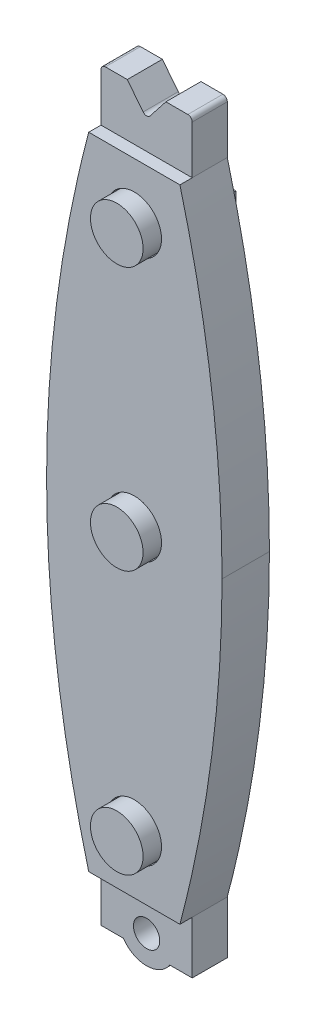
SolidWorks part; units mm, degrees
ref_plane "Front Plane" through (0, 0, 0) normal (0, 0, 1) x (1, 0, 0)
ref_plane "Top Plane" through (0, 0, 0) normal (0, 1, 0) x (1, 0, 0)
ref_plane "Right Plane" through (0, 0, 0) normal (1, 0, 0) x (0, 0, -1)
sketch "Sketch1" plane through (0, 0, 0) normal (0, 0, 1) x (1, 0, 0)
  line L1 (-33.062, 41.9494) -> (-7.662, 41.9494)
  line L2 (-33.062, 41.9494) -> (-33.062, -50.7606)
  line L3 (-33.062, -50.7606) -> (-7.662, -50.7606)
  line L4 (-7.662, 41.9494) -> (-7.662, -50.7606)
  dimension "D1" = 92.71
  dimension "D2" = 25.4
extrude "Boss-Extrude1" add sketch "Sketch1" along normal blind 5.08
sketch "Sketch3" plane through (0, -50.7606, 0) normal (0, -1, 0) x (1, 0, 0)
  line L0 (-7.662, 0) -> (-33.062, 5.08) construction
  line L1 (-33.062, 0) -> (-7.662, 0) construction
  line L2 (-13.758, 5.08) -> (-26.966, 5.08)
  line L3 (-13.758, 5.08) -> (-13.758, 0)
  line L4 (-13.758, 0) -> (-26.966, 0)
  line L5 (-26.966, 5.08) -> (-26.966, 0)
  line L6 (-13.758, 5.08) -> (-26.966, 0) construction
  line L7 (-13.758, 0) -> (-26.966, 5.08) construction
  point P4 (-20.362, 2.54)
  dimension "D1" = 13.208
extrude "Boss-Extrude3" add sketch "Sketch3" along normal blind 11.938
sketch "Sketch5" plane through (0, 0, 5.08) normal (0, 0, 1) x (1, 0, 0)
  line L0 (-23.7221, -58.3806) -> (-26.966, -58.3806)
  line L4 (-13.758, -62.6986) -> (-13.758, -58.3806)
  line L5 (-13.758, -58.3806) -> (-17.0019, -58.3806)
  line L6 (-13.758, -50.7606) -> (-7.662, -50.7606) construction
  line L8 (-26.966, -62.6986) -> (-26.966, -58.3806)
  line L9 (-13.758, -62.6986) -> (-26.966, -62.6986)
  circle A0 centre (-20.362, -56.0946) radius 1.905
  arc A1 (-23.7221, -58.3806) -> (-17.0019, -58.3806) centre (-20.362, -56.0946) ccw
  dimension "D2" = 3.81
  dimension "D3" = 8.128
  dimension "D4" = 7.62
extrude "Cut-Extrude2" cut sketch "Sketch5" against normal through all
sketch "Sketch7" plane through (0, 0, 5.08) normal (0, 0, 1) x (1, 0, 0)
  line L1 (-7.662, -50.7606) -> (-33.062, -50.7606)
  line L2 (-7.662, -50.7606) -> (-7.662, 41.9494)
  line L3 (-7.662, 41.9494) -> (-33.062, 41.9494)
  line L4 (-33.062, -50.7606) -> (-33.062, 41.9494)
extrude "Boss-Extrude4" add sketch "Sketch7" along normal blind 1.778
sketch "Sketch8" plane through (0, 0, 6.858) normal (0, 0, 1) x (1, 0, 0)
  line L0 (-33.062, -50.7606) -> (-7.662, -50.7606) construction
  circle A0 centre (-20.362, -42.3786) radius 3.937
  circle A1 centre (-20.362, -4.2786) radius 3.937
  circle A2 centre (-20.362, 33.8214) radius 3.937
  dimension "D1" = 7.874
  dimension "D2" = 8.382
  dimension "D3" = 3
extrude "Cut-Extrude3" cut sketch "Sketch8" against normal blind 1.27
sketch "Sketch10" plane through (0, 0, 5.588) normal (0, 0, 1) x (1, 0, 0)
  circle A0 centre (-20.362, -42.3786) radius 3.81
  circle A1 centre (-20.362, -4.2786) radius 3.81
  circle A2 centre (-20.362, 33.8214) radius 3.81
  dimension "D1" = 7.62
  dimension "D2" = 3
extrude "Boss-Extrude5" add sketch "Sketch10" along normal blind 3.81
sketch "Sketch11" plane through (0, 41.9494, 0) normal (0, 1, 0) x (1, 0, 0)
  line L0 (-20.362, 0) -> (-20.362, -6.858) construction
  line L1 (-7.662, 0) -> (-33.062, 0) construction
  line L2 (-7.662, -6.858) -> (-33.062, -6.858) construction
  line L4 (-13.758, -5.08) -> (-26.966, -5.08)
  line L5 (-13.758, -5.08) -> (-13.758, 0)
  line L6 (-13.758, 0) -> (-26.966, 0)
  line L7 (-26.966, -5.08) -> (-26.966, 0)
  line L8 (-13.758, -5.08) -> (-26.966, 0) construction
  line L9 (-13.758, 0) -> (-26.966, -5.08) construction
  point P6 (-20.362, -2.54)
  dimension "D1" = 13.208
  dimension "D2" = 5.08
  dimension "D3" = 0
extrude "Boss-Extrude6" add sketch "Sketch11" along normal blind 7.62
sketch "Sketch12" plane through (0, 0, 5.08) normal (0, 0, 1) x (1, 0, 0)
  line L0 (-26.966, 46.0134) -> (-13.758, 46.0134) construction
  line L1 (-26.966, 49.5694) -> (-26.966, 41.9494) construction
  line L2 (-13.758, 49.5694) -> (-13.758, 41.9494) construction
  line L3 (-23.156, 49.5694) -> (-23.156, 41.9494) construction
  line L4 (-26.966, 49.5694) -> (-13.758, 49.5694) construction
  line L5 (-26.966, 41.9494) -> (-13.758, 41.9494) construction
  line L6 (-17.568, 49.5694) -> (-17.568, 41.9494) construction
  line L7 (-7.662, 41.9494) -> (-33.062, 41.9494) construction
  line L8 (-20.362, 49.5694) -> (-20.362, 41.9494) construction
  line L9 (-23.156, 49.5694) -> (-20.362, 46.0134)
  line L10 (-20.362, 46.0134) -> (-17.568, 49.5694)
  line L11 (-17.568, 49.5694) -> (-23.156, 49.5694)
  dimension "D1" = 2.794
  dimension "D2" = 3.556
  dimension "D3" = 2.794
extrude "Cut-Extrude4" cut sketch "Sketch12" against normal through all
fillet "Fillet1" radius 0.635 3 edges at (-26.966, 49.5694, 2.54) (-20.362, 46.0134, 2.54) (-13.758, 49.5694, 2.54)
sketch "Sketch14" plane through (0, 0, 6.858) normal (0, 0, 1) x (1, 0, 0)
  line L0 (-7.662, -50.7606) -> (-7.662, 41.9494) construction
  line L1 (-33.062, 41.9494) -> (-33.062, -50.7606) construction
  line L2 (-13.758, 41.9494) -> (-7.662, 41.9494)
  line L3 (-7.662, 41.9494) -> (-7.662, -4.4056)
  line L4 (-33.062, -4.4056) -> (-33.062, 41.9494)
  line L6 (-33.062, 41.9494) -> (-26.966, 41.9494)
  spline S0 degree 2 poles (-13.758, 41.9494) (-7.662, 18.7719) (-7.662, -4.4056) knots 0 0 0 0.5 0.5 0.5
  spline S1 degree 2 poles (-26.966, 41.9494) (-33.062, 18.7719) (-33.062, -4.4056) knots 0 0 0 0.5 0.5 0.5
extrude "Cut-Extrude7" cut sketch "Sketch14" against normal blind 7.62
sketch "Sketch16" plane through (0, 0, 6.858) normal (0, 0, 1) x (1, 0, 0)
  line L1 (-33.062, -4.4056) -> (-33.062, -50.7606)
  line L2 (-33.062, -50.7606) -> (-26.966, -50.7606)
  line L3 (-7.662, -4.4056) -> (-7.662, -50.7606)
  line L4 (-7.662, -50.7606) -> (-13.758, -50.7606)
  spline S0 degree 2 poles (-13.758, -50.7606) (-7.662, -27.5831) (-7.662, -4.4056) knots 0 0 0 0.5 0.5 0.5
  spline S1 degree 2 poles (-33.062, -4.4056) (-33.062, -27.5831) (-26.966, -50.7606) knots 0.5 0.5 0.5 1 1 1
extrude "Cut-Extrude8" cut sketch "Sketch16" against normal through all
sketch "Sketch17" plane through (0, 0, 0) normal (0, 0, -1) x (-1, 0, 0)
  line L0 (7.662, -4.4056) -> (33.062, -4.4056) construction
  line L2 (14.012, -45.6806) -> (26.712, -45.6806)
  line L3 (14.012, -45.6806) -> (14.012, 36.8694)
  line L4 (14.012, 36.8694) -> (26.712, 36.8694)
  line L5 (26.712, -45.6806) -> (26.712, 36.8694)
  line L6 (14.012, -45.6806) -> (26.712, 36.8694) construction
  line L7 (14.012, 36.8694) -> (26.712, -45.6806) construction
  point P4 (20.362, -4.4056)
  dimension "D1" = 82.55
  dimension "D2" = 12.7
extrude "Boss-Extrude7" add sketch "Sketch17" along normal blind 1.524
